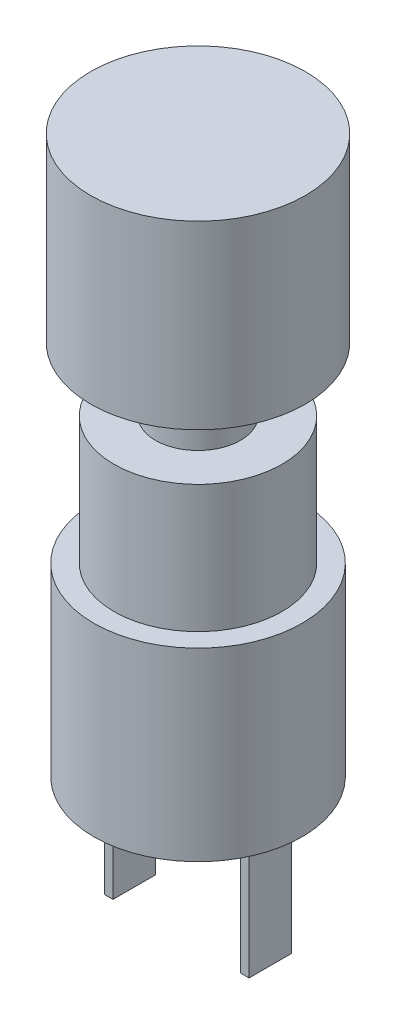
SolidWorks part; units mm, degrees
ref_plane "Plan de face" through (0, 0, 0) normal (0, 0, 1) x (1, 0, 0)
ref_plane "Plan de dessus" through (0, 0, 0) normal (0, 1, 0) x (1, 0, 0)
ref_plane "Plan de droite" through (0, 0, 0) normal (1, 0, 0) x (0, 0, -1)
sketch "Esquisse2" plane through (0, 0, 0) normal (0, 1, 0) x (1, 0, 0)
  circle A0 centre (0, 0) radius 4.9
  dimension "D1" = 9.8
extrude "Boss.-Extru.1" add sketch "Esquisse2" along normal blind 8.7
sketch "Esquisse3" plane through (0, 8.7, 0) normal (0, 1, 0) x (1, 0, 0)
  circle A0 centre (0, 0) radius 3.95
  dimension "D1" = 7.9
extrude "Boss.-Extru.2" add sketch "Esquisse3" along normal blind 6
sketch "Esquisse4" plane through (0, 14.7, 0) normal (0, 1, 0) x (1, 0, 0)
  circle A0 centre (0, 0) radius 2
  dimension "D1" = 4
extrude "Boss.-Extru.3" add sketch "Esquisse4" along normal blind 3
sketch "Esquisse5" plane through (0, 17.7, 0) normal (0, 1, 0) x (1, 0, 0)
  circle A0 centre (0, 0) radius 5.05
  dimension "D1" = 10.1
extrude "Boss.-Extru.4" add sketch "Esquisse5" along normal blind 8.5
sketch "Esquisse6" plane through (0, 0, 0) normal (0, -1, 0) x (1, 0, 0)
  line L1 (-3, -1) -> (-3.4, -1)
  line L2 (-3, -1) -> (-3, 1)
  line L3 (-3, 1) -> (-3.4, 1)
  line L4 (-3.4, -1) -> (-3.4, 1)
  line L5 (3, -1) -> (3.4, -1)
  line L6 (3, -1) -> (3, 1)
  line L7 (3, 1) -> (3.4, 1)
  line L8 (3.4, -1) -> (3.4, 1)
  dimension "D1" = 0.4
  dimension "D2" = 2
  dimension "D3" = 2
  dimension "D4" = 0.4
  dimension "D5" = 1
  dimension "D6" = 1
  dimension "D7" = 3
  dimension "D8" = 3
extrude "Boss.-Extru.5" add sketch "Esquisse6" along normal blind 6
